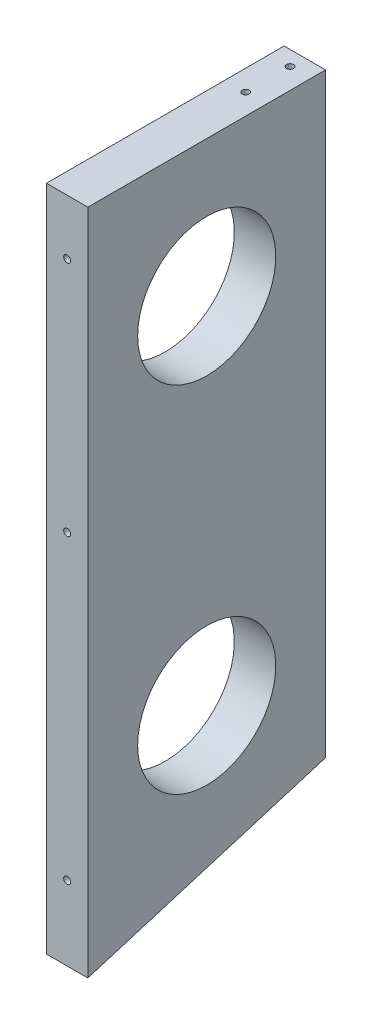
SolidWorks part; units mm, degrees
material "Beech"
ref_plane "Front Plane" through (0, 0, 0) normal (0, 0, 1) x (1, 0, 0)
ref_plane "Top Plane" through (0, 0, 0) normal (0, 1, 0) x (1, 0, 0)
ref_plane "Right Plane" through (0, 0, 0) normal (1, 0, 0) x (0, 0, -1)
sketch "Sketch1" plane through (0, 0, 0) normal (0, 0, 1) x (1, 0, 0)
  line L0 (-124.0045, -157.3) -> (-124.0045, -427.3421) construction
  line L1 (-124.0045, -157.3) -> (-124.0045, -144.6) construction
  line L2 (-244.0045, -144.6) -> (-4.0045, -144.6) construction
  line L7 (93.2955, -427.3421) -> (-341.3045, -427.3421) construction
  line L9 (8.6955, -157.3) -> (-256.7045, -157.3) construction
  line L10 (-133.5295, -157.3) -> (-133.5295, -427.3421)
  line L11 (-114.4795, -157.3) -> (-114.4795, -427.3421)
  line L12 (-133.5295, -157.3) -> (-114.4795, -157.3)
  line L13 (-133.5295, -427.3421) -> (-114.4795, -427.3421)
  dimension "D1" = 9.525
  dimension "D2" = 9.525
extrude "Boss-Extrude1" add sketch "Sketch1" along normal up to surface (33.95 mm away)
sketch "Sketch2" plane through (0, 0, 33.95) normal (0, 0, 1) x (1, 0, 0)
  line L0 (-256.7045, -157.3) -> (8.6955, -157.3) construction
  line L4 (-114.4795, -427.3421) -> (-114.4795, -157.3)
  line L5 (-114.4795, -157.3) -> (-133.5295, -157.3)
  line L6 (-133.5295, -157.3) -> (-133.5295, -427.3421)
  line L7 (-133.5295, -427.3421) -> (-114.4795, -427.3421)
  line L8 (-114.4795, -427.3421) -> (-114.4795, -157.3)
  line L9 (-114.4795, -157.3) -> (-133.5295, -157.3)
  line L10 (-133.5295, -157.3) -> (-133.5295, -427.3421)
  line L11 (-133.5295, -427.3421) -> (-114.4795, -427.3421)
  dimension "D1" = 0
extrude "Boss-Extrude2" add sketch "Sketch2" along normal up to surface (75.35 mm away)
sketch "Sketch3" plane through (-133.5295, 0, 0) normal (-1, 0, 0) x (0, 0, 1)
  line L0 (109.3, -427.3421) -> (109.3, -464.2661)
  line L1 (109.3, -464.2661) -> (0, -431.1858)
  line L2 (0, -431.1858) -> (0, -427.3421)
  line L3 (0, -427.3421) -> (109.3, -427.3421)
  line L4 (109.3, -427.3421) -> (0, -427.3421) construction
  line L5 (-12.7, -427.3421) -> (522.1409, -589.2145) construction
extrude "Boss-Extrude3" add sketch "Sketch3" against normal through all
hole_wizard "Hole1" positions "Sketch4" profile "Sketch5" legacy
sketch "Sketch4" plane through (-124.0045, 10.4243, 122) normal (0, 0, 1) x (-1, 0, 0)
  line L1 (0, 465.9538) -> (0, 167.7243) construction
  point P1 (113.65, 128.8076)
  point P3 (113.65, 23.941)
  point P5 (-94.6, 161.3743)
  point P7 (94.6, 161.3743)
  point P9 (0, 161.3743)
  point P11 (0, 193.1243)
  point P13 (0, 440.5538)
  point P15 (0, 301.9704)
  point P17 (40.9792, 301.9704)
  point P19 (166.7958, 301.9704)
  point P21 (207.775, 440.5538)
  point P23 (207.775, 333.0214)
  point P25 (207.775, 225.489)
  point P27 (207.775, 137.4243)
  point P29 (207.775, 10.4243)
  point P33 (-207.775, 10.4243)
  point P34 (-207.775, 137.4243)
  point P35 (-207.775, 225.489)
  point P36 (-207.775, 333.0214)
  point P37 (-207.775, 440.5538)
  point P38 (-166.7958, 301.9704)
  point P39 (-40.9792, 301.9704)
  point P40 (-113.65, 23.941)
  point P41 (-113.65, 128.8076)
sketch "Sketch5" plane through (-237.6545, -118.3833, 122) normal (1, 0, 0) x (0, -1, 0)
  line L0 (0, 0) -> (0, 32.7039)
  line L1 (0, 32.7039) -> (1.5875, 31.75)
  line L2 (1.5875, 31.75) -> (1.5875, 4.0177)
  line L3 (1.5875, 4.0177) -> (5.08, 0)
  line L4 (5.08, 0) -> (0, 0)
  line L5 (0, -14.3089) -> (0, 102.4216) construction
  line L6 (0, 32.7039) -> (-1.5875, 31.75) construction
  line L7 (-1.5875, 4.0177) -> (-5.08, 0) construction
  dimension "Diameter" = 3.175
  dimension "Depth" = 31.75
  dimension "C-Sink Diameter" = 10.16
  dimension "C-Sink Angle" = 82
  dimension "Drill Angle" = 118
hole_wizard "Hole3" positions "Sketch7" profile "Sketch8" legacy
sketch "Sketch7" plane through (-124.0045, -144.6, -155.2867) normal (0, 1, 0) x (-1, 0, 0)
  line L0 (0, 155.2867) -> (0, 189.2867) construction
  line L9 (0, 189.2867) -> (0, 182.4867)
  line L10 (0, 182.4867) -> (0, 175.6867)
  line L11 (0, 175.6867) -> (0, 168.8867)
  line L12 (0, 168.8867) -> (0, 162.0867)
  line L13 (0, 162.0867) -> (0, 155.2867)
  point P26 (0, 182.4867)
  point P32 (0, 162.0867)
sketch "Sketch8" plane through (-124.0045, -144.6, 6.8) normal (1, 0, 0) x (0, 0, 1)
  line L0 (0, 0) -> (0, 32.7039)
  line L1 (0, 32.7039) -> (1.5875, 31.75)
  line L2 (1.5875, 31.75) -> (1.5875, 4.0177)
  line L3 (1.5875, 4.0177) -> (5.08, 0)
  line L4 (5.08, 0) -> (0, 0)
  line L5 (0, -14.3089) -> (0, 102.4216) construction
  line L6 (0, 32.7039) -> (-1.5875, 31.75) construction
  line L7 (-1.5875, 4.0177) -> (-5.08, 0) construction
  dimension "Diameter" = 3.175
  dimension "Depth" = 31.75
  dimension "C-Sink Diameter" = 10.16
  dimension "C-Sink Angle" = 82
  dimension "Drill Angle" = 118
hole_wizard "Hole4" positions "Sketch9" profile "Sketch10" legacy
sketch "Sketch9" plane through (-124.0045, 10.4243, -12.7) normal (0, 0, -1) x (1, 0, 0)
  line L12 (0, 0) -> (0, 155.0243) construction
  point P0 (-207.775, 333.0214)
  point P3 (-207.775, 225.489)
  point P6 (-207.775, 137.4243)
  point P9 (-172.1667, 4.0743)
  point P12 (-146.0833, 4.0743)
  point P15 (-94.6, 161.3743)
  point P18 (0, 161.3743)
  point P21 (94.6, 161.3743)
  point P24 (146.0833, 4.0743)
  point P27 (172.1667, 4.0743)
  point P30 (207.775, 137.4243)
  point P33 (207.775, 225.489)
  point P36 (207.775, 333.0214)
  point P39 (166.7958, 301.9704)
  point P42 (40.9792, 301.9704)
  point P45 (-40.9792, 301.9704)
  point P48 (-166.7958, 301.9704)
  point P51 (0, 193.1243)
  point P54 (0, 301.9704)
  point P57 (0, 412.3664)
  point P80 (-126.35, 106.8243)
  point P82 (-126.35, 58.6243)
  point P96 (126.35, 58.6243)
  point P97 (126.35, 106.8243)
sketch "Sketch10" plane through (-331.7795, -322.5971, -12.7) normal (1, 0, 0) x (0, 1, 0)
  line L0 (0, 0) -> (0, 32.7039)
  line L1 (0, 32.7039) -> (1.5875, 31.75)
  line L2 (1.5875, 31.75) -> (1.5875, 4.0177)
  line L3 (1.5875, 4.0177) -> (5.08, 0)
  line L4 (5.08, 0) -> (0, 0)
  line L5 (0, -14.3089) -> (0, 102.4216) construction
  line L6 (0, 32.7039) -> (-1.5875, 31.75) construction
  line L7 (-1.5875, 4.0177) -> (-5.08, 0) construction
  dimension "Diameter" = 3.175
  dimension "Depth" = 31.75
  dimension "C-Sink Diameter" = 10.16
  dimension "C-Sink Angle" = 82
  dimension "Drill Angle" = 118
hole_wizard "Hole5" positions "Sketch11" profile "Sketch12" legacy
sketch "Sketch11" plane through (-124.0045, -363.2296, -268.3751) normal (0, -0.9571, -0.2897) x (1, 0, 0)
  line L4 (-207.775, 822.0847) -> (-207.775, 404.0189) construction
  line L8 (-207.775, 822.0847) -> (-207.775, 717.5683)
  line L9 (-207.775, 717.5683) -> (-207.775, 613.0518)
  line L10 (-207.775, 613.0518) -> (-207.775, 508.5353)
  line L11 (-207.775, 508.5353) -> (-207.775, 404.0189)
  line L12 (-108.65, 822.0847) -> (-108.65, 404.0189) construction
  line L15 (0, 822.0847) -> (0, 613.0518) construction
  line L18 (-207.775, 390.7499) -> (-207.775, 276.5537) construction
  line L22 (-207.775, 390.7499) -> (-207.775, 362.2009)
  line L23 (-207.775, 362.2009) -> (-207.775, 333.6518)
  line L24 (-207.775, 333.6518) -> (-207.775, 305.1027)
  line L25 (-207.775, 305.1027) -> (-207.775, 276.5537)
  line L26 (0, 390.7499) -> (0, 276.5537) construction
  line L30 (0, 276.5537) -> (0, 305.1027)
  line L31 (0, 305.1027) -> (0, 333.6518)
  line L32 (0, 333.6518) -> (0, 362.2009)
  line L33 (0, 362.2009) -> (0, 390.7499)
  point P24 (-207.775, 613.0518)
  point P31 (-207.775, 456.2771)
  point P33 (-207.775, 769.8265)
  point P52 (-108.65, 456.2771)
  point P54 (-108.65, 630.1265)
  point P56 (-108.65, 769.8265)
  point P76 (-207.775, 362.2009)
  point P80 (-207.775, 305.1027)
  point P99 (0, 305.1027)
  point P104 (0, 362.2009)
  point P113 (207.775, 305.1027)
  point P114 (207.775, 362.2009)
  point P115 (108.65, 769.8265)
  point P116 (108.65, 630.1265)
  point P117 (108.65, 456.2771)
  point P118 (207.775, 769.8265)
  point P119 (207.775, 456.2771)
  point P120 (207.775, 613.0518)
  dimension "D1" = 139.7
sketch "Sketch12" plane through (83.7705, -540.8176, 318.3915) normal (1, 0, 0) x (0, 0.2897, -0.9571)
  line L0 (0, 0) -> (0, 32.7039)
  line L1 (0, 32.7039) -> (1.5875, 31.75)
  line L2 (1.5875, 31.75) -> (1.5875, 4.0177)
  line L3 (1.5875, 4.0177) -> (5.08, 0)
  line L4 (5.08, 0) -> (0, 0)
  line L5 (0, -14.3089) -> (0, 102.4216) construction
  line L6 (0, 32.7039) -> (-1.5875, 31.75) construction
  line L7 (-1.5875, 4.0177) -> (-5.08, 0) construction
  dimension "Diameter" = 3.175
  dimension "Depth" = 31.75
  dimension "C-Sink Diameter" = 10.16
  dimension "C-Sink Angle" = 82
  dimension "Drill Angle" = 118
hole_wizard "Hole6" positions "Sketch13" profile "Sketch15" legacy end condition up to next
sketch "Sketch13" plane through (-133.5295, 0, 0) normal (-1, 0, 0) x (0, 0, 1)
  line L0 (109.3, -157.3) -> (109.3, -282.7961) construction
  line L1 (109.3, -157.3) -> (109.3, -464.2661) construction
  line L3 (109.3, -301.8461) -> (109.3, -464.2661) construction
  line L5 (0, -431.1858) -> (109.3, -464.2661) construction
  line L6 (109.3, -220.048) -> (0, -220.048) construction
  line L7 (0, -157.3) -> (0, -431.1858) construction
  line L9 (109.3, -383.0561) -> (0, -383.0561) construction
  point P0 (54.65, -220.048)
  point P28 (54.65, -383.0561)
sketch "Sketch15" plane through (-133.5295, -220.048, 54.65) normal (0, 1, 0) x (0, 0, 1)
  line L0 (0, 0) -> (0, 19.05)
  line L1 (0, 19.05) -> (31.75, 19.05)
  line L2 (31.75, 19.05) -> (31.75, 0)
  line L3 (31.75, 0) -> (0, 0)
  line L4 (0, 110) -> (0, -10) construction
  dimension "Diameter" = 63.5
  dimension "Depth" = 19.05
